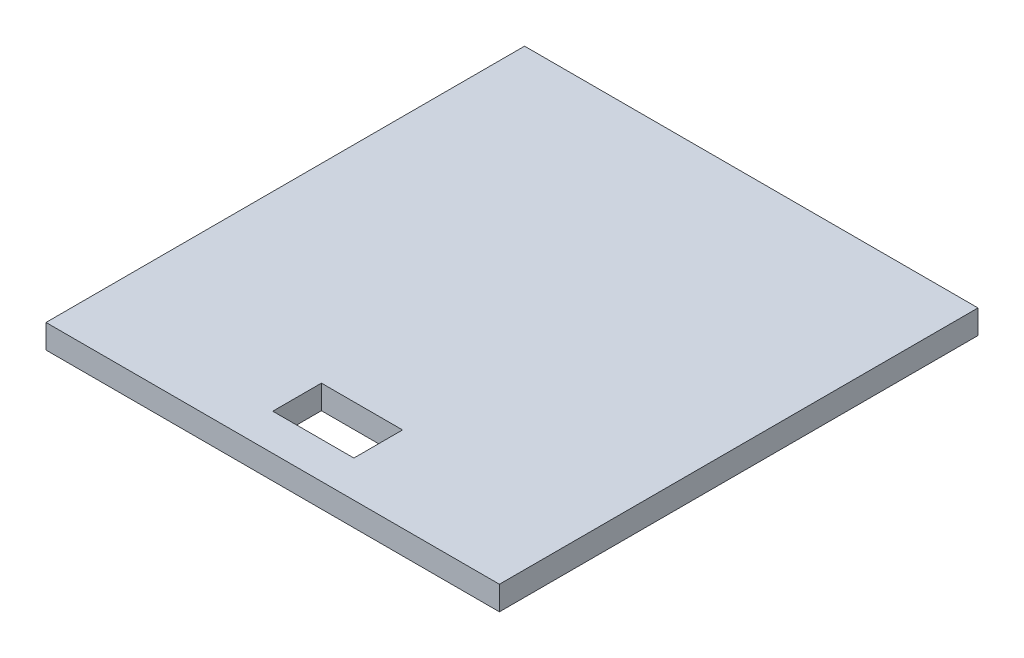
SolidWorks part; units mm, degrees
ref_plane "Front Plane" through (0, 0, 0) normal (0, 0, 1) x (1, 0, 0)
ref_plane "Top Plane" through (0, 0, 0) normal (0, 1, 0) x (1, 0, 0)
ref_plane "Right Plane" through (0, 0, 0) normal (1, 0, 0) x (0, 0, -1)
sketch "Sketch1" plane through (0, 0, 0) normal (0, 1, 0) x (1, 0, 0)
  line L1 (-45.0739, 26.7241) -> (10.8261, 26.7241)
  line L2 (-45.0739, 26.7241) -> (-45.0739, -32.2759)
  line L3 (-45.0739, -32.2759) -> (10.8261, -32.2759)
  line L4 (10.8261, 26.7241) -> (10.8261, -32.2759)
  dimension "D1" = 55.9
  dimension "D2" = 59
extrude "Boss-Extrude1" add sketch "Sketch1" along normal blind 2.95
sketch "Sketch4" plane through (0, 2.95, 0) normal (0, 1, 0) x (1, 0, 0)
  line L0 (-45.0739, -32.2759) -> (10.8261, -32.2759) construction
  line L1 (-21.619, -21.7759) -> (-11.619, -21.7759)
  line L2 (-21.619, -21.7759) -> (-21.619, -27.7759)
  line L3 (-21.619, -27.7759) -> (-11.619, -27.7759)
  line L4 (-11.619, -21.7759) -> (-11.619, -27.7759)
  point P4 (-16.619, -27.7759)
  dimension "D1" = 6
  dimension "D2" = 10
  dimension "D3" = 4.5
extrude "Cut-Extrude2" cut sketch "Sketch4" against normal blind 6.86
